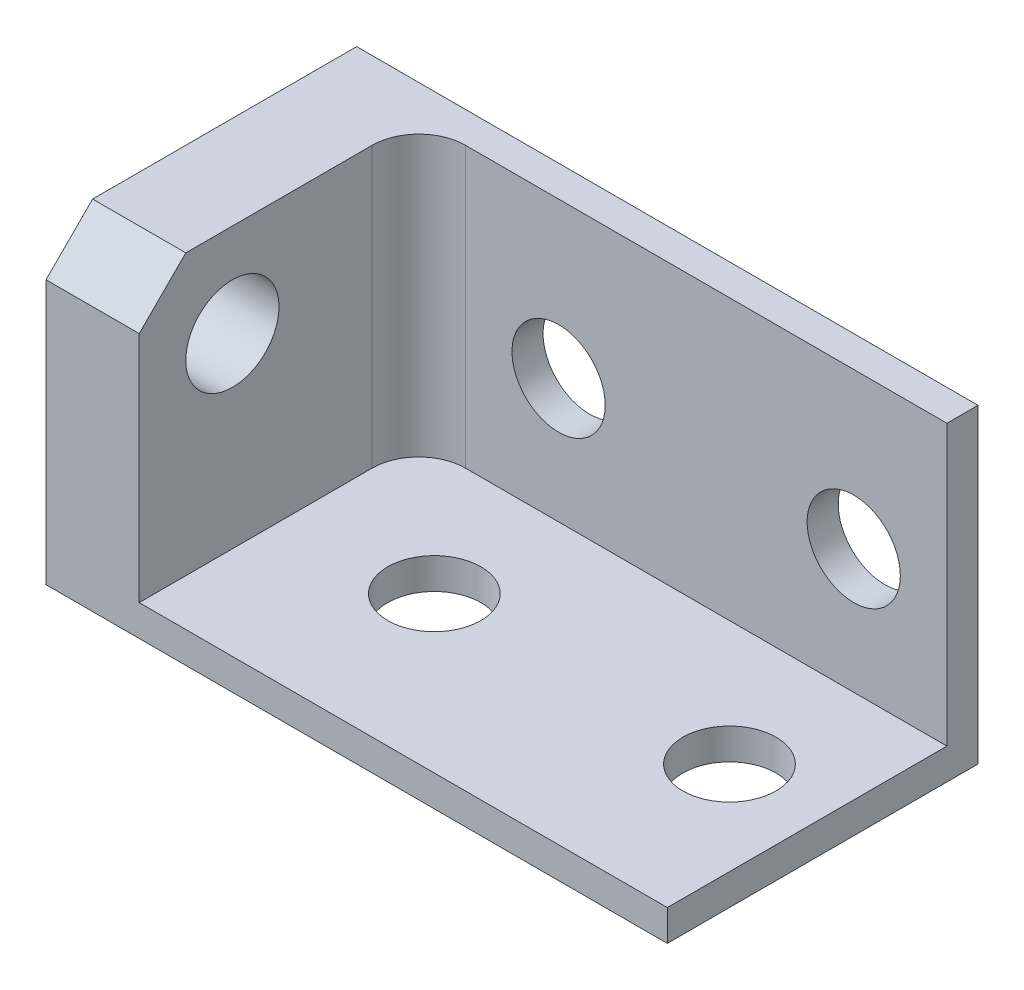
SolidWorks part; units mm, degrees
ref_plane "Plan de face" through (0, 0, 0) normal (0, 0, 1) x (1, 0, 0)
ref_plane "Plan de dessus" through (0, 0, 0) normal (0, 1, 0) x (1, 0, 0)
ref_plane "Plan de droite" through (0, 0, 0) normal (1, 0, 0) x (0, 0, -1)
sketch "Esquisse1" plane through (0, 0, 0) normal (0, 0, 1) x (1, 0, 0)
  line L1 (0, 0) -> (-40, 0)
  line L2 (0, 0) -> (0, 20)
  line L3 (0, 20) -> (-40, 20)
  line L4 (-40, 0) -> (-40, 20)
  dimension "D1" = 40
  dimension "D2" = 20
extrude "Boss.-Extru.1" add sketch "Esquisse1" along normal blind 2
sketch "Esquisse2" plane through (0, 0, 2) normal (0, 0, 1) x (1, 0, 0)
  line L0 (-40, 20) -> (-40, 0) construction
  line L1 (0, 0) -> (-40, 0)
  line L2 (0, 0) -> (0, 2)
  line L3 (0, 2) -> (-40, 2)
  line L4 (-40, 0) -> (-40, 2)
  dimension "D1" = 2
extrude "Boss.-Extru.2" add sketch "Esquisse2" along normal blind 18
sketch "Esquisse3" plane through (0, 0, 2) normal (0, 0, 1) x (1, 0, 0)
  line L0 (0, 20) -> (-40, 20) construction
  line L1 (0, 2) -> (0, 20) construction
  circle A0 centre (-6, 10) radius 3
  dimension "D1" = 6
  dimension "D2" = 10
  dimension "D3" = 6
extrude "Enlèv. mat.-Extru.1" cut sketch "Esquisse3" against normal blind 18
sketch "Esquisse4" plane through (0, 0, 2) normal (0, 0, 1) x (1, 0, 0)
  line L0 (0, 20) -> (-40, 20) construction
  line L1 (0, 2) -> (0, 20) construction
  circle A0 centre (-25, 10) radius 3
  dimension "D1" = 6
  dimension "D2" = 10
  dimension "D3" = 25
extrude "Enlèv. mat.-Extru.2" cut sketch "Esquisse4" against normal blind 18
sketch "Esquisse5" plane through (0, 2, 0) normal (0, 1, 0) x (1, 0, 0)
  line L0 (0, -20) -> (-40, -20) construction
  line L1 (0, -20) -> (0, -2) construction
  circle A0 centre (-6, -10) radius 3
  dimension "D1" = 6
  dimension "D2" = 10
  dimension "D3" = 6
extrude "Enlèv. mat.-Extru.3" cut sketch "Esquisse5" against normal blind 18
sketch "Esquisse6" plane through (0, 2, 0) normal (0, 1, 0) x (1, 0, 0)
  line L0 (0, -20) -> (-40, -20) construction
  line L1 (0, -20) -> (0, -2) construction
  circle A0 centre (-25, -10) radius 3
  dimension "D1" = 6
  dimension "D2" = 10
  dimension "D3" = 25
extrude "Enlèv. mat.-Extru.4" cut sketch "Esquisse6" against normal blind 18
sketch "Esquisse7" plane through (0, 2, 0) normal (0, 1, 0) x (1, 0, 0)
  line L0 (0, -20) -> (-40, -20) construction
  line L1 (-40, -2) -> (-34, -2)
  line L2 (-40, -2) -> (-40, -20)
  line L3 (-40, -20) -> (-34, -20)
  line L4 (-34, -2) -> (-34, -20)
  dimension "D1" = 6
extrude "Boss.-Extru.3" add sketch "Esquisse7" along normal blind 18
sketch "Esquisse8" plane through (-40, 0, 0) normal (-1, 0, 0) x (0, 0, 1)
  line L0 (20, 20) -> (20, 0) construction
  line L1 (20, 20) -> (0, 20) construction
  circle A0 centre (14, 14) radius 3
  dimension "D1" = 6
  dimension "D2" = 6
  dimension "D3" = 6
extrude "Enlèv. mat.-Extru.5" cut sketch "Esquisse8" against normal blind 18
chamfer "Chanfrein1" distance 3 angle 45 1 edges at (-37, 20, 20)
fillet "Congé1" radius 3 1 edges at (-34, 11, 2)
